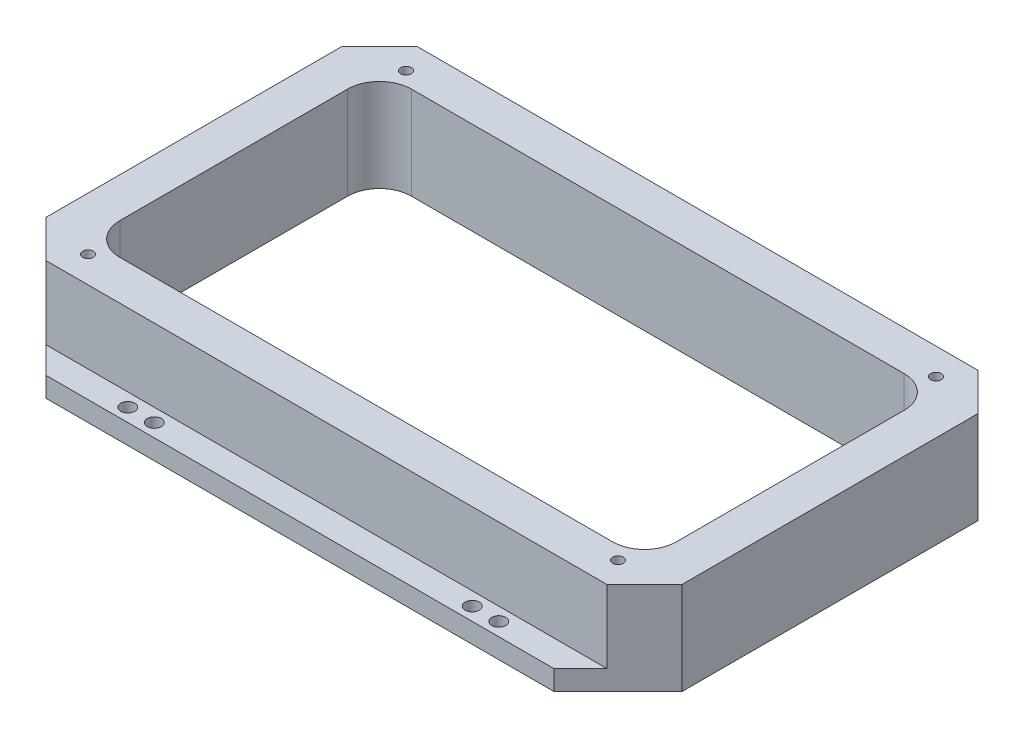
SolidWorks part; units mm, degrees
material "Al 6061-T6"
ref_plane "Front Plane" through (0, 0, 0) normal (0, 0, 1) x (1, 0, 0)
ref_plane "Top Plane" through (0, 0, 0) normal (0, 1, 0) x (1, 0, 0)
ref_plane "Right Plane" through (0, 0, 0) normal (1, 0, 0) x (0, 0, -1)
sketch "Sketch1" plane through (0, 0, 0) normal (0, 1, 0) x (1, 0, 0)
  line L1 (152.4, -88.9) -> (-152.4, -88.9)
  line L2 (152.4, -88.9) -> (152.4, 88.9)
  line L3 (152.4, 88.9) -> (-152.4, 88.9)
  line L4 (-152.4, -88.9) -> (-152.4, 88.9)
  line L5 (152.4, -88.9) -> (-152.4, 88.9) construction
  line L6 (152.4, 88.9) -> (-152.4, -88.9) construction
  point P0 (0, 0)
  dimension "D1" = 304.8
  dimension "D2" = 177.8
extrude "Boss-Extrude1" add sketch "Sketch1" along normal blind 44.45
chamfer "Chamfer1" distance 17.9578 angle 45 4 edges at (-152.4, 22.225, -88.9) (152.4, 22.225, -88.9) (152.4, 22.225, 88.9) (-152.4, 22.225, 88.9)
sketch "Sketch3" plane through (0, 44.45, 0) normal (0, 1, 0) x (1, 0, 0)
  line L0 (-126.5514, 69.85) -> (-133.35, 63.0514)
  line L1 (-133.35, 63.0514) -> (-133.35, -63.0514)
  line L2 (-133.35, -63.0514) -> (-126.5514, -69.85)
  line L3 (-126.5514, -69.85) -> (126.5514, -69.85)
  line L4 (126.5514, -69.85) -> (133.35, -63.0514)
  line L5 (133.35, -63.0514) -> (133.35, 63.0514)
  line L6 (133.35, 63.0514) -> (126.5514, 69.85)
  line L7 (126.5514, 69.85) -> (-126.5514, 69.85)
  line L8 (134.4422, 88.9) -> (-134.4422, 88.9)
  line L9 (-134.4422, 88.9) -> (-152.4, 70.9422)
  line L10 (-152.4, 70.9422) -> (-152.4, -70.9422)
  line L11 (-152.4, -70.9422) -> (-134.4422, -88.9)
  line L12 (-134.4422, -88.9) -> (134.4422, -88.9)
  line L13 (134.4422, -88.9) -> (152.4, -70.9422)
  line L14 (152.4, -70.9422) -> (152.4, 70.9422)
  line L15 (152.4, 70.9422) -> (134.4422, 88.9)
  line L16 (134.4422, 88.9) -> (-134.4422, 88.9)
  line L17 (-134.4422, 88.9) -> (-152.4, 70.9422)
  line L18 (-152.4, 70.9422) -> (-152.4, -70.9422)
  line L19 (-152.4, -70.9422) -> (-134.4422, -88.9)
  line L20 (-134.4422, -88.9) -> (134.4422, -88.9)
  line L21 (134.4422, -88.9) -> (152.4, -70.9422)
  line L22 (152.4, -70.9422) -> (152.4, 70.9422)
  line L23 (152.4, 70.9422) -> (134.4422, 88.9)
  line L25 (133.35, -69.85) -> (-133.35, -69.85)
  line L26 (133.35, -69.85) -> (133.35, 69.85)
  line L27 (133.35, 69.85) -> (-133.35, 69.85)
  line L28 (-133.35, -69.85) -> (-133.35, 69.85)
  line L29 (133.35, -69.85) -> (-133.35, 69.85) construction
  line L30 (133.35, 69.85) -> (-133.35, -69.85) construction
  point P16 (0, 0)
  dimension "D1" = 0
  dimension "D2" = 19.05
extrude "Cut-Extrude1" cut sketch "Sketch3" against normal through all contours L6 L7 L0 L1 L2 L3 L4 L5 | L28 L0 L27 | L26 L27 L6 | L28 L25 L2 | L25 L26 L4
hole_wizard "1/4-20 Tapped Hole1" positions "Sketch4" profile "Sketch5" tap size "1/4-20" standard "ANSI Inch"
sketch "Sketch4" plane through (0, 44.45, 0) normal (0, 1, 0) x (1, 0, 0)
  line L0 (0, 88.9) -> (0, -88.9) construction
  line L1 (134.4422, 88.9) -> (-134.4422, 88.9) construction
  line L2 (-134.4422, -88.9) -> (134.4422, -88.9) construction
  line L4 (-152.4, 0) -> (152.4, 0) construction
  line L5 (-152.4, 70.9422) -> (-152.4, -70.9422) construction
  line L6 (152.4, -70.9422) -> (152.4, 70.9422) construction
  point P0 (-127, 76.2)
  point P23 (127, 76.2)
  point P24 (127, -76.2)
  point P25 (-127, -76.2)
  dimension "D1" = 127
  dimension "D2" = 76.2
  dimension "D3" = 2
  dimension "D4" = 2
sketch "Sketch5" plane through (-127, 44.45, -76.2) normal (1, 0, 0) x (0, 0, 1)
  line L0 (0, 0) -> (0, 20.5838)
  line L1 (0, 20.5838) -> (2.5527, 19.05)
  line L2 (2.5527, 19.05) -> (2.5527, 0)
  line L5 (2.5527, 0) -> (0, 0)
  line L10 (0, 20.5838) -> (-2.5527, 19.05) construction
  line L11 (0, -6.35) -> (0, 107.95) construction
  dimension "Tap Drill Dia." = 5.1054
  dimension "Tap Drill Depth" = 19.05
  dimension "Drill Angle" = 118
cosmetic thread "Hole Thread1" parameters "D1"=12.7, "D2"=6.35
cosmetic thread "Hole Thread2" parameters "D1"=12.7, "D2"=6.35
cosmetic thread "Hole Thread3" parameters "D1"=12.7, "D2"=6.35
cosmetic thread "Hole Thread4" parameters "D1"=12.7, "D2"=6.35
sketch "Sketch6" plane through (0, 0, 0) normal (0, -1, 0) x (1, 0, 0)
  line L0 (-134.4422, 88.9) -> (-121.7422, 101.6)
  line L1 (-121.7422, 101.6) -> (121.7422, 101.6)
  line L2 (121.7422, 101.6) -> (134.4422, 88.9)
  line L8 (-152.4, 70.9422) -> (-152.4, -70.9422)
  line L9 (-152.4, -70.9422) -> (-134.4422, -88.9)
  line L10 (-134.4422, -88.9) -> (134.4422, -88.9)
  line L11 (134.4422, -88.9) -> (152.4, -70.9422)
  line L12 (152.4, -70.9422) -> (152.4, 70.9422)
  line L13 (152.4, 70.9422) -> (134.4422, 88.9)
  line L14 (134.4422, 88.9) -> (-134.4422, 88.9)
  line L15 (-134.4422, 88.9) -> (-152.4, 70.9422)
  line L16 (-152.4, 70.9422) -> (-152.4, -70.9422)
  line L17 (-152.4, -70.9422) -> (-134.4422, -88.9)
  line L18 (-134.4422, -88.9) -> (134.4422, -88.9)
  line L19 (134.4422, -88.9) -> (152.4, -70.9422)
  line L20 (152.4, -70.9422) -> (152.4, 70.9422)
  line L21 (152.4, 70.9422) -> (134.4422, 88.9)
  line L22 (134.4422, 88.9) -> (-134.4422, 88.9)
  line L23 (-134.4422, 88.9) -> (-152.4, 70.9422)
  line M26 (134.4422, 88.9) -> (-134.4422, 88.9)
  dimension "D2" = 101.6
  dimension "D1" = 0
extrude "Boss-Extrude2" add sketch "Sketch6" against normal blind 9.525 contours L2 L1 L0 M26
hole_wizard "1/4 Clearance Hole1" positions "Sketch7" profile "Sketch8" hole size "1/4" standard "ANSI Inch" end condition through all
sketch "Sketch7" plane through (0, 9.525, 0) normal (0, 1, 0) x (1, 0, 0)
  line L8 (121.7422, -101.6) -> (134.4422, -88.9)
  line L9 (134.4422, -88.9) -> (-134.4422, -88.9)
  line L10 (-134.4422, -88.9) -> (-121.7422, -101.6)
  line L11 (-121.7422, -101.6) -> (121.7422, -101.6)
  line L12 (121.7422, -101.6) -> (134.4422, -88.9)
  line L13 (134.4422, -88.9) -> (-134.4422, -88.9)
  line L14 (-134.4422, -88.9) -> (-121.7422, -101.6)
  line L15 (-121.7422, -101.6) -> (121.7422, -101.6)
  line L16 (0, -101.6) -> (0, -88.9) construction
  point P0 (-88.9, -95.25)
  point P2 (88.9, -95.25)
  point P24 (-76.2, -95.25)
  point P26 (76.2, -95.25)
  dimension "D2" = 6.35
  dimension "D3" = 88.9
  dimension "D4" = 88.9
  dimension "D5" = 76.2
  dimension "D6" = 76.2
  dimension "D1" = 0
sketch "Sketch8" plane through (-88.9, 9.525, 95.25) normal (1, 0, 0) x (0, 0, 1)
  line L0 (0, 0) -> (0, 9.525)
  line L1 (0, 9.525) -> (3.3782, 9.525)
  line L2 (3.3782, 9.525) -> (3.3782, 0)
  line L5 (3.3782, 0) -> (0, 0)
  line L11 (0, -6.35) -> (0, 107.95) construction
  dimension "Thru Hole Dia." = 6.7564
  dimension "Thru Hole Depth" = 9.525
mirror "Mirror1" about plane through (0, 0, 0) normal (0, 0, 1) of "1/4 Clearance Hole1", "Boss-Extrude2"
fillet "Fillet2" radius 15.24 4 edges at (133.35, 22.225, 69.85) (-133.35, 22.225, 69.85) (-133.35, 22.225, -69.85) (133.35, 22.225, -69.85)
